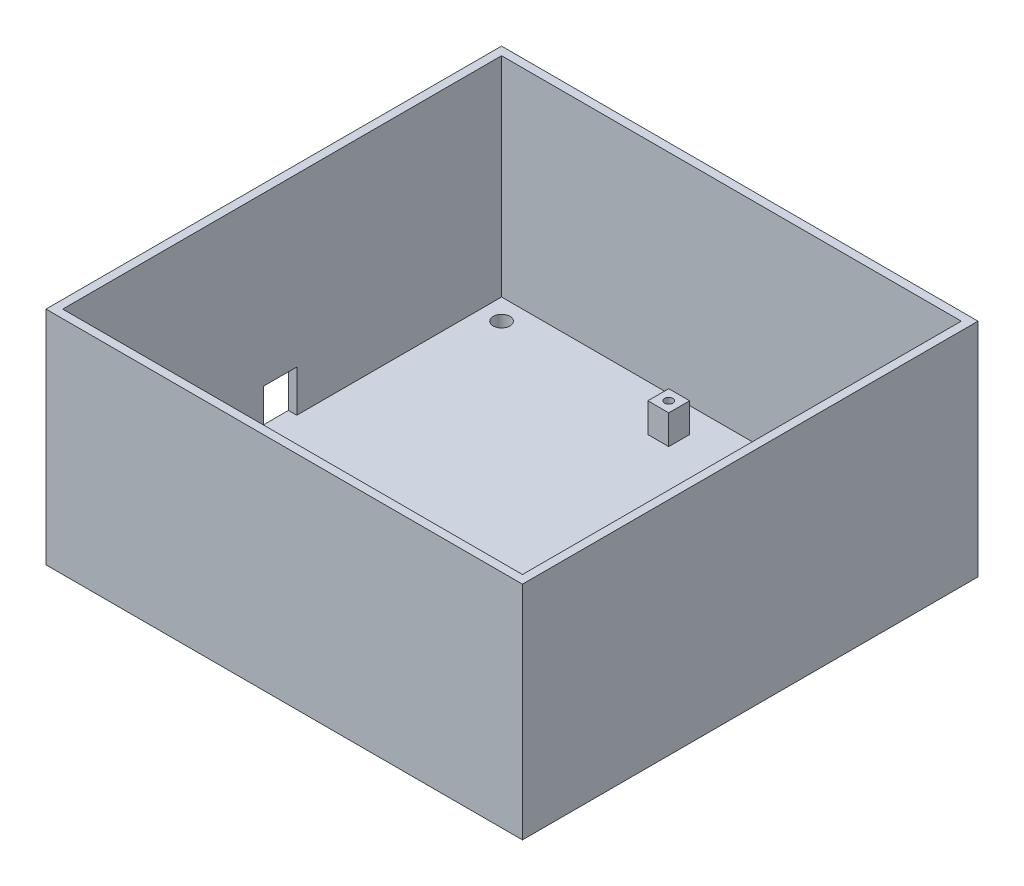
SolidWorks part; units mm, degrees
ref_plane "Front Plane" through (0, 0, 0) normal (0, 0, 1) x (1, 0, 0)
ref_plane "Top Plane" through (0, 0, 0) normal (0, 1, 0) x (1, 0, 0)
ref_plane "Right Plane" through (0, 0, 0) normal (1, 0, 0) x (0, 0, -1)
sketch "Sketch1" plane through (0, 0, 0) normal (0, 1, 0) x (1, 0, 0)
  line L1 (-57, 52) -> (57, 52)
  line L2 (-57, 52) -> (-57, -52)
  line L3 (-57, -52) -> (57, -52)
  line L4 (57, 52) -> (57, -52)
  line L5 (-57, 52) -> (57, -52) construction
  line L6 (-57, -52) -> (57, 52) construction
  point P0 (0, 0)
  dimension "D1" = 114
  dimension "D2" = 104
extrude "Boss-Extrude1" add sketch "Sketch1" along normal blind 3
sketch "Sketch2" plane through (0, 3, 0) normal (0, 1, 0) x (1, 0, 0)
  line L0 (57, 52) -> (-57, 52) construction
  line L1 (55, -50) -> (-55, -50)
  line L2 (55, -50) -> (55, 50)
  line L3 (55, 50) -> (-55, 50)
  line L4 (-55, -50) -> (-55, 50)
  line L5 (55, -50) -> (-55, 50) construction
  line L6 (55, 50) -> (-55, -50) construction
  line L7 (-57, 52) -> (-57, -52) construction
  line L9 (57, -52) -> (-57, -52)
  line L10 (57, -52) -> (57, 52)
  line L11 (57, 52) -> (-57, 52)
  line L12 (-57, -52) -> (-57, 52)
  line L13 (57, -52) -> (-57, 52) construction
  line L14 (57, 52) -> (-57, -52) construction
  point P0 (0, 0)
  point P10 (0, 0)
  dimension "D1" = 2
  dimension "D2" = 2
extrude "Boss-Extrude2" add sketch "Sketch2" along normal blind 50
sketch "Sketch3" plane through (0, 3, 0) normal (0, 1, 0) x (1, 0, 0)
  line L0 (-55, -50) -> (55, -50) construction
  line L1 (55, 50) -> (-15, 50)
  line L2 (55, 50) -> (55, -50)
  line L3 (55, -50) -> (-15, -50)
  line L4 (-15, 50) -> (-15, -50)
  line L5 (55, 50) -> (-55, 50) construction
  line L6 (-4, 39) -> (-9, 39)
  line L7 (-4, 39) -> (-4, 44)
  line L8 (-4, 44) -> (-9, 44)
  line L9 (-9, 39) -> (-9, 44)
  line L10 (-4, 39) -> (-9, 44) construction
  line L11 (-4, 44) -> (-9, 39) construction
  line L12 (-4, -44) -> (-9, -44)
  line L13 (-4, -44) -> (-4, -39)
  line L14 (-4, -39) -> (-9, -39)
  line L15 (-9, -44) -> (-9, -39)
  line L16 (-4, -44) -> (-9, -39) construction
  line L17 (-4, -39) -> (-9, -44) construction
  line L18 (55, 44) -> (50, 44)
  line L19 (55, 44) -> (55, 49)
  line L20 (55, 49) -> (50, 49)
  line L21 (50, 44) -> (50, 49)
  line L22 (55, 44) -> (50, 49) construction
  line L23 (55, 49) -> (50, 44) construction
  line L24 (40, -44) -> (35, -44)
  line L25 (40, -44) -> (40, -39)
  line L26 (40, -39) -> (35, -39)
  line L27 (35, -44) -> (35, -39)
  line L28 (40, -44) -> (35, -39) construction
  line L29 (40, -39) -> (35, -44) construction
  point P7 (-6.5, 41.5)
  point P12 (-6.5, -41.5)
  point P17 (52.5, 46.5)
  point P22 (37.5, -41.5)
  dimension "D1" = 70
  dimension "D2" = 6
  dimension "D3" = 6
  dimension "D4" = 5
  dimension "D5" = 5
  dimension "D6" = 5
  dimension "D7" = 5
  dimension "D8" = 6
  dimension "D9" = 6
  dimension "D10" = 5
  dimension "D11" = 5
  dimension "D12" = 6
  dimension "D13" = 15
  dimension "D14" = 5
  dimension "D15" = 5
  dimension "D16" = 1
  dimension "D17" = 0
extrude "Boss-Extrude4" add sketch "Sketch3" along normal blind 7 contours L9 L6 L7 L8 | L21 L18 L2 L20 | L15 L12 L13 L14 | L27 L24 L25 L26
sketch "Sketch8" plane through (0, 0, 52) normal (0, 0, 1) x (1, 0, 0)
  line L1 (-57, 53) -> (57, 53)
  line L2 (-57, 53) -> (-57, 0)
  line L3 (-57, 0) -> (57, 0)
  line L4 (57, 53) -> (57, 0)
extrude "Boss-Extrude6" add sketch "Sketch8" along normal blind 5
sketch "Sketch9" plane through (0, 0, 50) normal (0, 0, -1) x (-1, 0, 0)
  line L1 (-55, 53) -> (55, 53)
  line L2 (-55, 53) -> (-55, 3)
  line L3 (-55, 3) -> (55, 3)
  line L4 (55, 53) -> (55, 3)
extrude "Cut-Extrude2" cut sketch "Sketch9" against normal blind 5
sketch "Sketch10" plane through (0, 10, 0) normal (0, 1, 0) x (1, 0, 0)
  line L1 (55, 50) -> (-15, 50)
  line L2 (55, 50) -> (55, -50)
  line L3 (55, -50) -> (-15, -50)
  line L4 (-15, 50) -> (-15, -50)
  dimension "D1" = 100
  dimension "D2" = 70
sketch "Sketch12" plane through (-55, 0, 0) normal (1, 0, 0) x (0, 0, -1)
  line L0 (50, 3) -> (-55, 3) construction
  line L1 (1, 3) -> (-7, 3)
  line L2 (1, 3) -> (1, 13)
  line L3 (1, 13) -> (-7, 13)
  line L4 (-7, 3) -> (-7, 13)
  line L5 (-55, 3) -> (-55, 53) construction
  line L6 (50, 53) -> (50, 3) construction
  dimension "D1" = 8
  dimension "D2" = 10
  dimension "D3" = 48
  dimension "D4" = 49
extrude "Cut-Extrude3" cut sketch "Sketch12" against normal up to surface (2 mm away) up to face at (-57, 26.5, 2.5)
sketch "Sketch14" plane through (0, 10, 0) normal (0, 1, 0) x (1, 0, 0)
  line L0 (-6.5, 44) -> (-6.5, 39) construction
  line L1 (-4, 44) -> (-9, 44) construction
  line L2 (-4, 39) -> (-9, 39) construction
  line L3 (52.5, 49) -> (52.5, 44) construction
  line L4 (55, 49) -> (50, 49) construction
  line L5 (55, 44) -> (50, 44) construction
  line L6 (-6.5, -39) -> (-6.5, -44) construction
  line L7 (-4, -39) -> (-9, -39) construction
  line L8 (-4, -44) -> (-9, -44) construction
  line L9 (37.5, -39) -> (37.5, -44) construction
  line L10 (40, -39) -> (35, -39) construction
  line L11 (40, -44) -> (35, -44) construction
  circle A0 centre (-6.5, 41.5) radius 1
  circle A1 centre (-6.5, -41.5) radius 1
  circle A2 centre (37.5, -41.5) radius 1
  circle A3 centre (52.5, 46.5) radius 1
  dimension "D1" = 2
extrude "Cut-Extrude5" cut sketch "Sketch14" against normal blind 3
sketch "Sketch15" plane through (0, 3, 0) normal (0, 1, 0) x (1, 0, 0)
  line L0 (55, 50) -> (-55, 50) construction
  line L1 (-55, 50) -> (-55, 1) construction
  line L3 (55, -55) -> (-55, -55) construction
  circle A0 centre (-50, 45) radius 2
  circle A1 centre (-50, -50) radius 2
  circle A2 centre (43.81, -50) radius 2
  circle A3 centre (43.81, 45) radius 2
  point P12 (0, 0)
  point P13 (0, 0)
  point P14 (0, 0)
  point P15 (0, 0)
  point P16 (0, 0)
  dimension "D1" = 5
  dimension "D2" = 5
  dimension "D3" = 4
  dimension "D4" = 5
extrude "Cut-Extrude6" cut sketch "Sketch15" against normal up to surface (3 mm away) up to face at (0, 0, 2.5)
